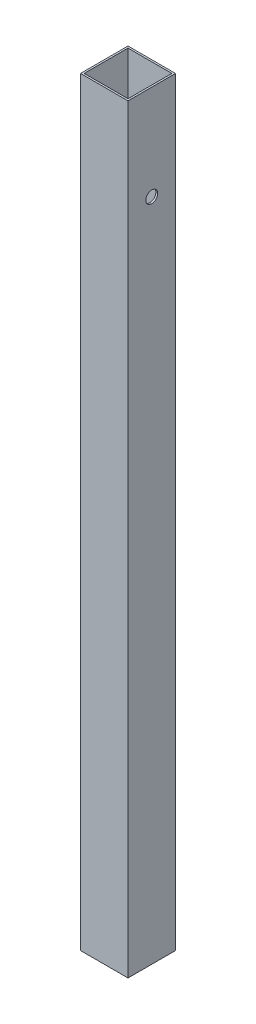
SolidWorks part; units mm, degrees
ref_plane "Front Plane" through (0, 0, 0) normal (0, 0, 1) x (1, 0, 0)
ref_plane "Top Plane" through (0, 0, 0) normal (0, 1, 0) x (1, 0, 0)
ref_plane "Right Plane" through (0, 0, 0) normal (1, 0, 0) x (0, 0, -1)
sketch "Sketch1" plane through (0, 0, 0) normal (0, 1, 0) x (1, 0, 0)
  line L0 (-11.7348, -11.7348) -> (11.7348, -11.7348)
  line L1 (-12.7, 12.7) -> (12.7, 12.7)
  line L2 (-12.7, 12.7) -> (-12.7, -12.7)
  line L3 (-12.7, -12.7) -> (12.7, -12.7)
  line L4 (12.7, 12.7) -> (12.7, -12.7)
  line L5 (-12.7, 12.7) -> (12.7, -12.7) construction
  line L6 (-12.7, -12.7) -> (12.7, 12.7) construction
  line L7 (11.7348, 11.7348) -> (11.7348, -11.7348)
  line L8 (-11.7348, 11.7348) -> (11.7348, 11.7348)
  line L9 (-11.7348, 11.7348) -> (-11.7348, -11.7348)
  point P0 (0, 0)
  dimension "D1" = 25.4
  dimension "D2" = 25.4
  dimension "D3" = 0.9652
extrude "Boss-Extrude1" add sketch "Sketch1" along normal blind 406.4
sketch "Sketch3" plane through (-12.7, 0, 0) normal (-1, 0, 0) x (0, 0, 1)
  line L0 (12.7, 406.4) -> (12.7, 0) construction
  circle A0 centre (0, 355.6) radius 3.175
  dimension "D1" = 355.6
  dimension "D3" = 6.35
  dimension "D2" = 12.7
extrude "Cut-Extrude1" cut sketch "Sketch3" against normal blind 406.4
